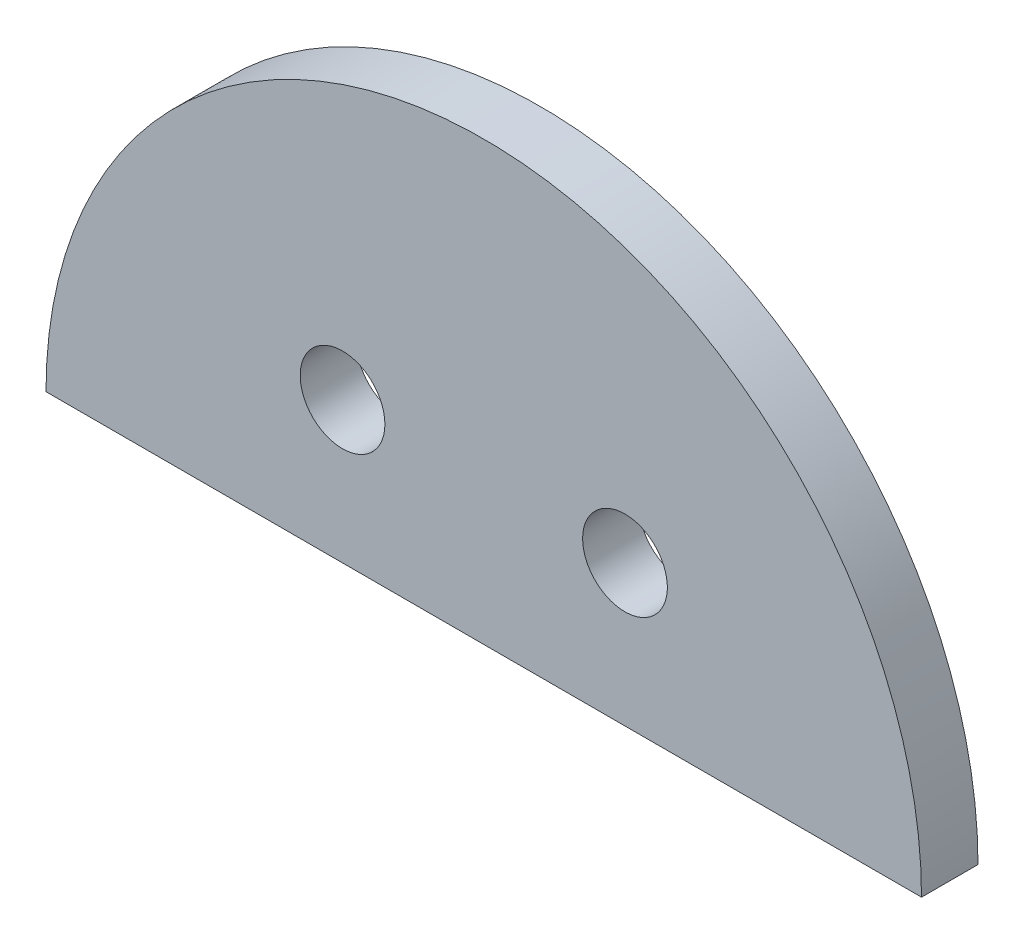
SolidWorks part; units mm, degrees
ref_plane "前视基准面" through (0, 0, 0) normal (0, 0, 1) x (1, 0, 0)
ref_plane "上视基准面" through (0, 0, 0) normal (0, 1, 0) x (1, 0, 0)
ref_plane "右视基准面" through (0, 0, 0) normal (1, 0, 0) x (0, 0, -1)
sketch "草图1" plane through (0, 0, 0) normal (0, 0, 1) x (1, 0, 0)
  line L0 (-15.5, 0) -> (15.5, 0)
  line L1 (-14.6714, 5) -> (14.6714, 5) construction
  line L2 (0, 0) -> (0, 15.5) construction
  circle A0 centre (-5, 5) radius 1.5
  arc A1 (15.5, 0) -> (-15.5, 0) centre (0, 0) ccw
  circle A2 centre (5, 5) radius 1.5
  dimension "D1" = 15.5
  dimension "D2" = 3
  dimension "D3" = 10
  dimension "D4" = 5
extrude "凸台-拉伸1" add sketch "草图1" along normal blind 2
